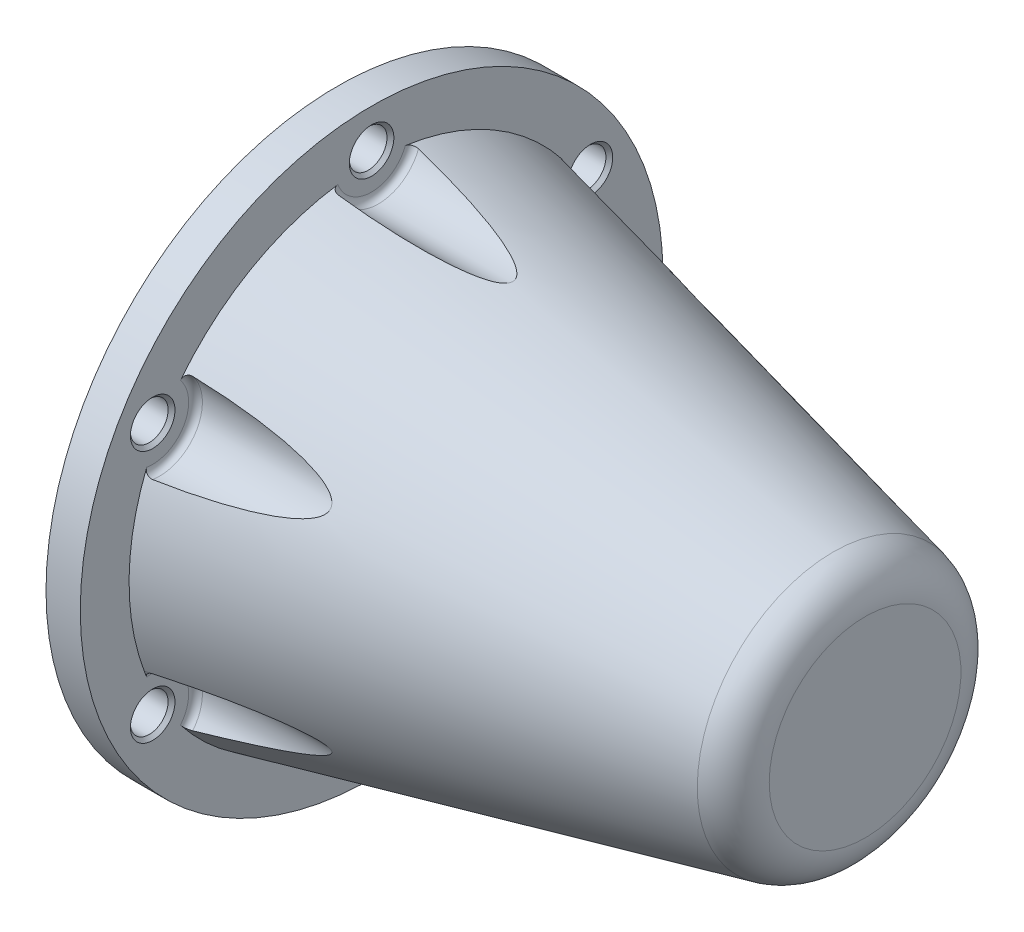
SolidWorks part; units mm, degrees
material "16NiCr4"
ref_plane "Płaszczyzna przednia" through (0, 0, 0) normal (0, 0, 1) x (1, 0, 0)
ref_plane "Płaszczyzna górna" through (0, 0, 0) normal (0, 1, 0) x (1, 0, 0)
ref_plane "Płaszczyzna prawa" through (0, 0, 0) normal (1, 0, 0) x (0, 0, -1)
sketch "Szkic1" plane through (0, 0, 0) normal (0, 0, 1) x (1, 0, 0)
  line L0 (0, 0) -> (154, 0) construction
  line L1 (154, 0) -> (154, 37.518)
  line L2 (154, 37.518) -> (10, 70.763)
  line L3 (10, 70.763) -> (10, 85)
  line L4 (10, 85) -> (0, 85)
  line L5 (0, 85) -> (0, 60.5)
  line L6 (0, 60.5) -> (10, 60.5)
  line L7 (10, 60.5) -> (144, 29.5637)
  line L8 (144, 29.5637) -> (144, 0)
  line L9 (154, 0) -> (144, 0)
  dimension "D1" = 13
  dimension "D2" = 170
  dimension "D3" = 121
  dimension "D4" = 154
  dimension "D5" = 10
  dimension "D6" = 10
  dimension "D7" = 10
revolve "Obrót1" add sketch "Szkic1" angle 360 about L0
sketch "Szkic2" plane through (10, 0, 0) normal (1, 0, 0) x (0, 0, -1)
  circle A0 centre (0, 0) radius 73.75 construction
  circle A1 centre (0, 73.75) radius 12.5
  dimension "D1" = 147.5
  dimension "D2" = 25
extrude "Wytnij-wyciągnięcie1" cut sketch "Szkic2" along normal up to next (134 mm away)
hole_wizard "Otwór pod śrubę M101" positions "Szkic4" profile "Szkic3" hole size "M10" standard "Iso" end condition through all
sketch "Szkic4" plane through (10, 0, 0) normal (1, 0, 0) x (0, 0, -1)
  point P0 (0, 73.75)
sketch "Szkic3" plane through (10, 73.75, 0) normal (0, 1, 0) x (0, 0, -1)
  line L0 (0, 0) -> (0, 10)
  line L1 (0, 10) -> (6.5, 10)
  line L2 (5.5, 9) -> (5.5, 1)
  line L3 (5.5, 1) -> (6.5, 0)
  line L5 (6.5, 0) -> (0, 0)
  line L6 (-5.5, 1) -> (-6.5, 0) construction
  line L7 (6.5, 10) -> (5.5, 9)
  line L8 (-6.5, 10) -> (-5.5, 9) construction
  line L11 (0, -6.35) -> (0, 107.95) construction
  dimension "Średnica otworu na wylot" = 11
  dimension "Głębokość otworu na wylot" = 10
  dimension "Średnica zewnętrznego pogłębienia stożkowego" = 13
  dimension "Kąt zewnętrznego pogłębienia stożkowego" = 90
  dimension "Średnica wewnętrznego pogłębienia stożkowego" = 13
  dimension "Kąt wewnętrznego pogłębienia stożkowego" = 90
pattern_circular "Szyk kołowy1" count 6 over 360 about axis through (0, 0, 0) along (1, 0, 0) of "Wytnij-wyciągnięcie1", "Otwór pod śrubę M101"
fillet "Zaokrąglenie1" radius 12 1 edges at (154, 0, 37.518)
fillet "Zaokrąglenie2" radius 2 6 edges at (10, -30.625, -53.0441) (10, -61.25, 0) (10, -30.625, 53.0441) (10, 30.625, 53.0441) (10, 61.25, 0) (10, 30.625, -53.0441)
fillet "Zaokrąglenie3" radius 2 1 edges at (144, 0, 29.5637)
chamfer "Sfazowanie1" distance 1 angle 45 1 edges at (0, 0, 60.5)
